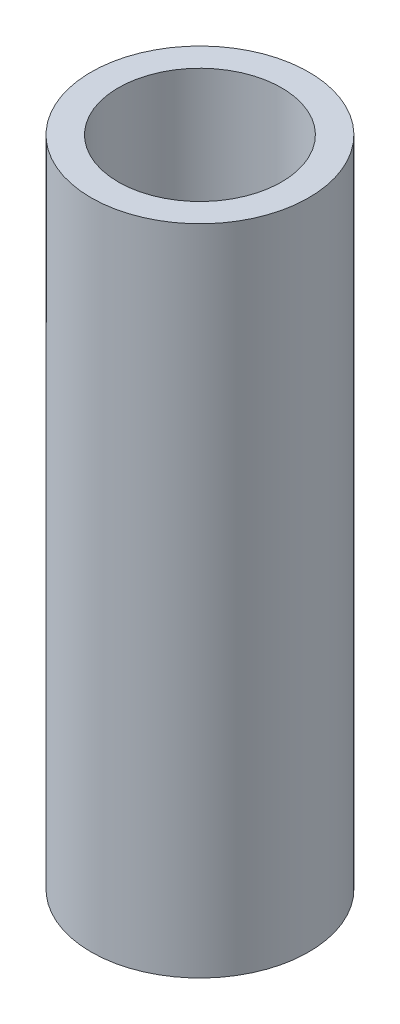
SolidWorks part; units mm, degrees
ref_plane "Front Plane" through (0, 0, 0) normal (0, 0, 1) x (1, 0, 0)
ref_plane "Top Plane" through (0, 0, 0) normal (0, 1, 0) x (1, 0, 0)
ref_plane "Right Plane" through (0, 0, 0) normal (1, 0, 0) x (0, 0, -1)
sketch "Sketch1" plane through (0, 0, 0) normal (0, 1, 0) x (1, 0, 0)
  circle A0 centre (0, 0) radius 12.7
  circle A1 centre (0, 0) radius 9.525
  dimension "D1" = 19.05
  dimension "D2" = 25.4
extrude "Boss-Extrude2" add sketch "Sketch1" along normal blind 76.2
